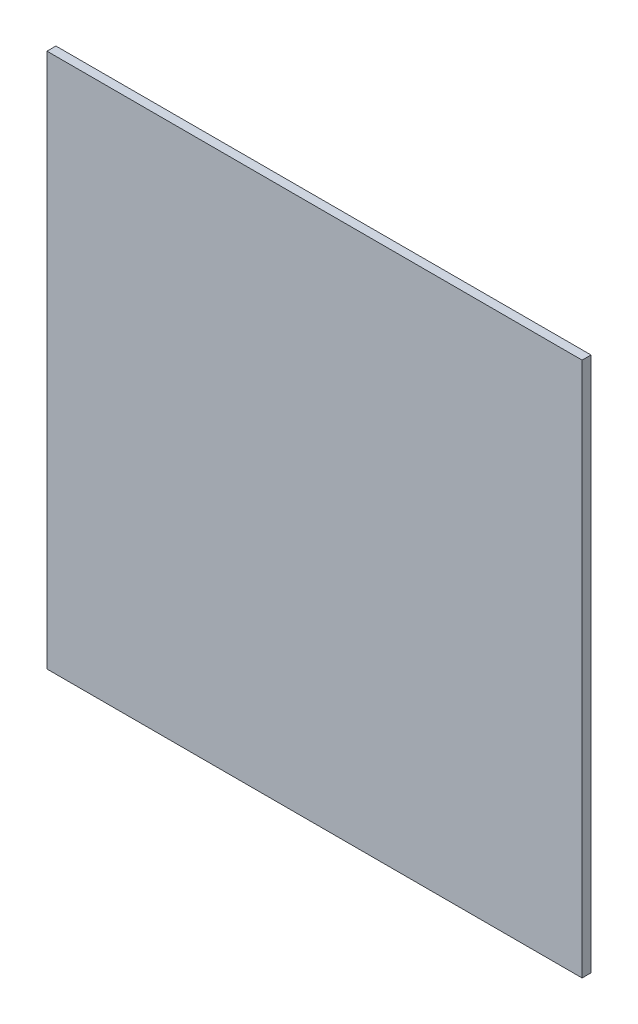
SolidWorks part; units mm, degrees
ref_plane "前视基准面" through (0, 0, 0) normal (0, 0, 1) x (1, 0, 0)
ref_plane "上视基准面" through (0, 0, 0) normal (0, 1, 0) x (1, 0, 0)
ref_plane "右视基准面" through (0, 0, 0) normal (1, 0, 0) x (0, 0, -1)
sketch "草图1" plane through (0, 0, 0) normal (0, 0, 1) x (1, 0, 0)
  line L1 (0, 0) -> (180, 0)
  line L2 (0, 0) -> (0, 180)
  line L3 (0, 180) -> (180, 180)
  line L4 (180, 0) -> (180, 180)
extrude "凸台-拉伸1" add sketch "草图1" along normal blind 3
